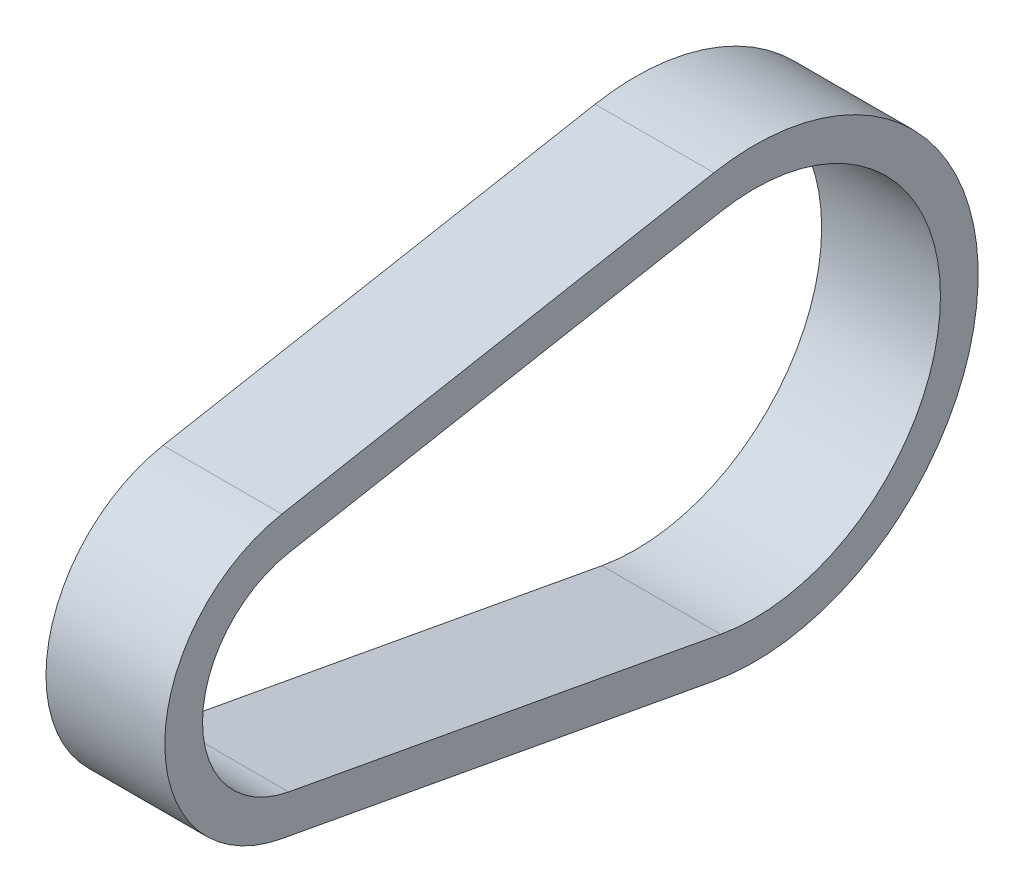
SolidWorks part; units mm, degrees
ref_plane "Front Plane" through (0, 0, 0) normal (0, 0, 1) x (1, 0, 0)
ref_plane "Top Plane" through (0, 0, 0) normal (0, 1, 0) x (1, 0, 0)
ref_plane "Right Plane" through (0, 0, 0) normal (1, 0, 0) x (0, 0, -1)
other "Bounding Box"
ref_plane "Default Plane" through (-8.9266, -12.7485, 0) normal (-0.1736, 0.9848, 0) x (0.9848, 0.1736, 0)
sketch "Sketch1" plane through (0, 0, 0) normal (1, 0, 0) x (0, 0, -1)
  line L0 (0, 0) -> (56.3956, 0) construction
  line L1 (-2.4046, 13.0648) -> (52.1432, 23.1044)
  line L2 (-2.4046, -13.0648) -> (52.1432, -23.1044)
  line L3 (-3.2667, 17.7486) -> (51.2811, 27.7882)
  line L4 (-3.2667, -17.7486) -> (51.2811, -27.7882)
  line L5 (-13.2842, 0) -> (-18.0467, 0) construction
  line L6 (79.8881, 0) -> (84.6506, 0) construction
  arc A0 (-2.4046, 13.0648) -> (-2.4046, -13.0648) centre (0, 0) ccw
  arc A1 (52.1432, -23.1044) -> (52.1432, 23.1044) centre (56.3956, 0) ccw
  arc A2 (-3.2667, 17.7486) -> (-3.2667, -17.7486) centre (0, 0) ccw
  arc A3 (51.2811, -27.7882) -> (51.2811, 27.7882) centre (56.3956, 0) ccw
  dimension "D2" = 4.7625
  dimension "D4" = 26.5684
  dimension "D5" = 46.9849
  dimension "D1" = 56.3956
extrude "Boss-Extrude1" add sketch "Sketch1" along normal mid plane 15
